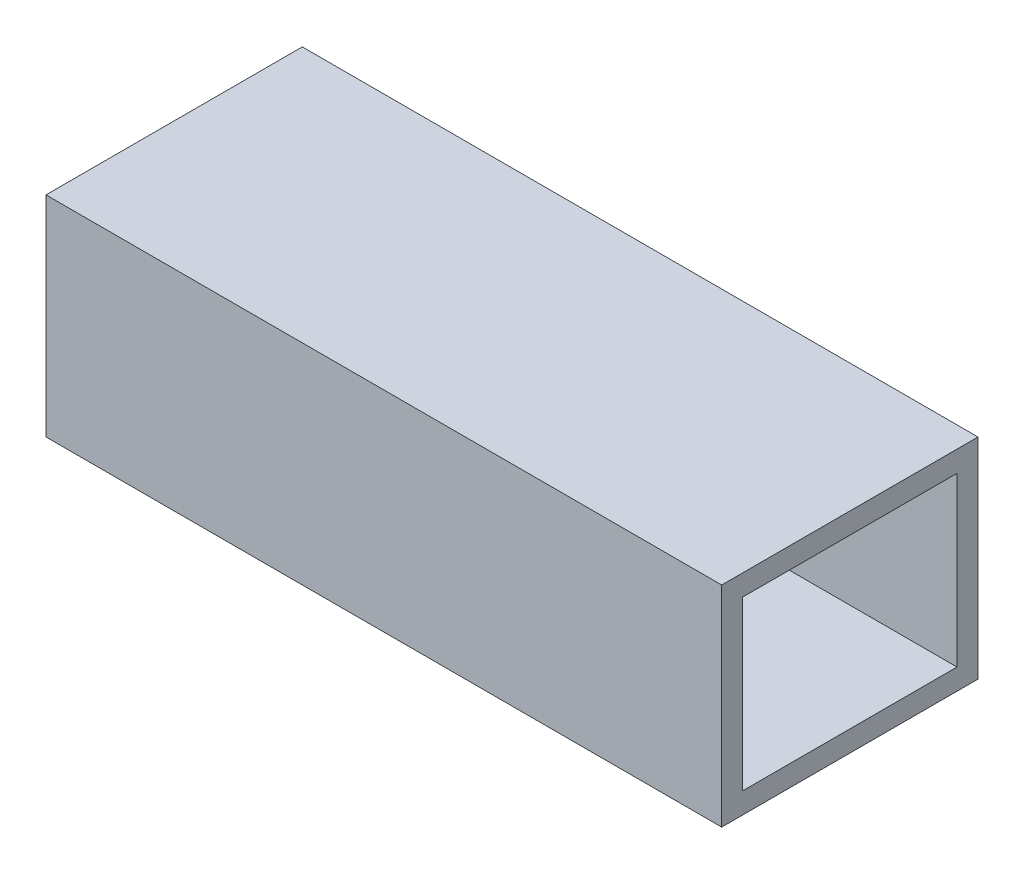
SolidWorks part; units mm, degrees
ref_plane "Front Plane" through (0, 0, 0) normal (0, 0, 1) x (1, 0, 0)
ref_plane "Top Plane" through (0, 0, 0) normal (0, 1, 0) x (1, 0, 0)
ref_plane "Right Plane" through (0, 0, 0) normal (1, 0, 0) x (0, 0, -1)
sketch "Sketch1" plane through (0, 0, 0) normal (0, 0, 1) x (1, 0, 0)
  line L1 (0, 0) -> (145, 0)
  line L2 (0, 0) -> (0, 45)
  line L3 (0, 45) -> (145, 45)
  line L4 (145, 0) -> (145, 45)
  dimension "D1" = 45
  dimension "D2" = 145
extrude "Boss-Extrude1" add sketch "Sketch1" along normal blind 55
sketch "Sketch2" plane through (145, 0, 0) normal (1, 0, 0) x (0, 0, -1)
  line L0 (-27.5, 45) -> (-27.5, 0) construction
  line L1 (-55, 45) -> (0, 45) construction
  line L2 (-55, 0) -> (0, 0) construction
  line L3 (-50.5, 40.5) -> (-4.5, 40.5)
  line L4 (-50.5, 40.5) -> (-50.5, 4.5)
  line L5 (-50.5, 4.5) -> (-4.5, 4.5)
  line L6 (-4.5, 40.5) -> (-4.5, 4.5)
  line L7 (0, 22.5) -> (-55, 22.5) construction
  line L8 (0, 0) -> (0, 45) construction
  line L9 (-55, 0) -> (-55, 45) construction
  point P16 (0, 0)
  point P17 (-27.5, 4.5)
  point P18 (0, 0)
  point P19 (-50.5, 22.5)
  dimension "D1" = 46
  dimension "D2" = 36
extrude "Cut-Extrude1" cut sketch "Sketch2" against normal blind 130
sketch "Sketch3" plane through (0, 0, 55) normal (0, 0, 1) x (1, 0, 0)
  line L0 (0, 45) -> (0, 0) construction
  line L1 (0, 22.5) -> (145, 22.5)
  line L2 (0, 22.5) -> (0, 13.1324)
  line L3 (0, 13.1324) -> (145, 13.1324)
  line L4 (145, 22.5) -> (145, 13.1324)
  line L5 (145, 0) -> (145, 45) construction
